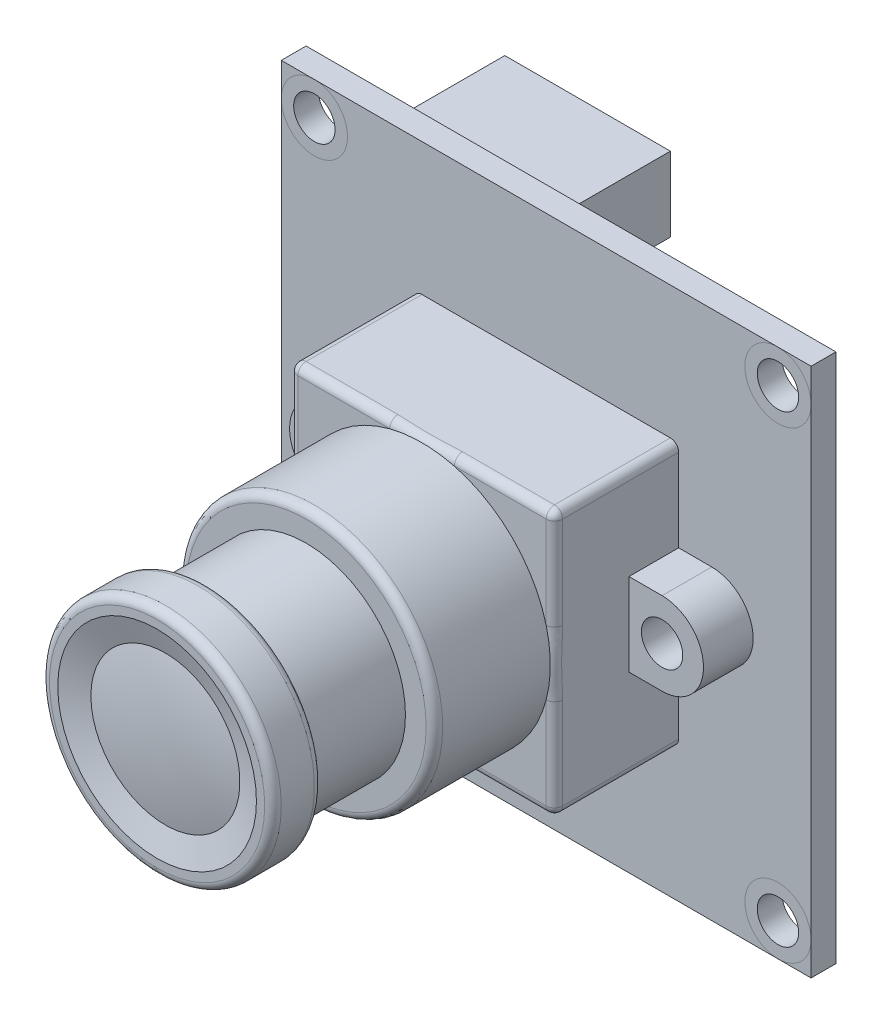
SolidWorks part; units mm, degrees
ref_plane "Front" through (0, 0, 0) normal (0, 0, 1) x (1, 0, 0)
ref_plane "Top" through (0, 0, 0) normal (0, 1, 0) x (1, 0, 0)
ref_plane "Right" through (0, 0, 0) normal (1, 0, 0) x (0, 0, -1)
sketch "Sketch1" plane through (0, 0, 0) normal (0, 0, 1) x (1, 0, 0)
  line L1 (-16, -16) -> (16, -16)
  line L2 (-16, -16) -> (-16, 16)
  line L3 (-16, 16) -> (16, 16)
  line L4 (16, -16) -> (16, 16)
  line L5 (-16, -16) -> (16, 16) construction
  line L6 (-16, 16) -> (16, -16) construction
  point P0 (0, 0)
  dimension "D1" = 32
extrude "Boss-Extrude1" add sketch "Sketch1" along normal blind 1.5
sketch "Sketch2" plane through (0, 0, 1.5) normal (0, 0, 1) x (1, 0, 0)
  line L0 (0, 16) -> (0, -16) construction
  line L1 (16, 16) -> (-16, 16) construction
  line L2 (-16, -16) -> (16, -16) construction
  line L3 (16, 0) -> (-16, 0) construction
  line L4 (16, -16) -> (16, 16) construction
  line L5 (-16, 16) -> (-16, -16) construction
  line L6 (-14, 14) -> (-14, 16) construction
  line L7 (-14, 14) -> (-16, 14) construction
  circle A0 centre (-14, 14) radius 1.25
  circle A1 centre (14, 14) radius 1.25
  circle A2 centre (14, -14) radius 1.25
  circle A3 centre (-14, -14) radius 1.25
  point P26 (0, 0)
  dimension "D1" = 2.5
  dimension "D2" = 28
  dimension "D3" = 4
extrude "Cut-Extrude1" cut sketch "Sketch2" against normal through all
sketch "Sketch3" plane through (0, 0, 1.5) normal (0, 0, 1) x (1, 0, 0)
  line L1 (8, -8) -> (-8, -8)
  line L2 (8, -8) -> (8, 8)
  line L3 (8, 8) -> (-8, 8)
  line L4 (-8, -8) -> (-8, 8)
  line L5 (8, -8) -> (-8, 8) construction
  line L6 (8, 8) -> (-8, -8) construction
  point P0 (0, 0)
  dimension "D1" = 16
extrude "Boss-Extrude2" add sketch "Sketch3" along normal blind 7.5
sketch "Sketch4" plane through (0, 0, 1.5) normal (0, 0, 1) x (1, 0, 0)
  line L0 (0, 0) -> (-10, 0) construction
  line L1 (-10, 2.5) -> (-8, 2.5)
  line L2 (-8, 8) -> (-8, -8) construction
  line L3 (-10, -2.5) -> (-8, -2.5)
  line L4 (-8, 2.5) -> (-8, -2.5)
  line L5 (0, 0) -> (0, 8) construction
  line L6 (8, 8) -> (-8, 8) construction
  line L7 (10, -2.5) -> (8, -2.5)
  line L8 (8, 2.5) -> (8, -2.5)
  line L9 (10, 2.5) -> (8, 2.5)
  circle A0 centre (-10, 0) radius 1.25
  circle A1 centre (-10, 0) radius 2.5 construction
  arc A2 (-10, 2.5) -> (-10, -2.5) centre (-10, 0) ccw
  circle A3 centre (10, 0) radius 1.25
  arc A4 (10, 2.5) -> (10, -2.5) centre (10, 0) cw
  point P5 (-9, 2.5)
  dimension "D2" = 2.5
  dimension "D3" = 5
  dimension "D1" = 10
extrude "Boss-Extrude3" add sketch "Sketch4" along normal blind 3
sketch "Sketch5" plane through (0, 0, 9) normal (0, 0, 1) x (1, 0, 0)
  circle A0 centre (0, 0) radius 7.75
  dimension "D1" = 15.5
extrude "Boss-Extrude4" add sketch "Sketch5" along normal blind 7
sketch "Sketch6" plane through (0, 0, 16) normal (0, 0, 1) x (1, 0, 0)
  circle A0 centre (0, 0) radius 6
  dimension "D1" = 12
extrude "Boss-Extrude5" add sketch "Sketch6" along normal blind 6
sketch "Sketch8" plane through (0, 0, 0) normal (0, 1, 0) x (1, 0, 0)
  line L0 (0, -22) -> (-7, -22)
  line L1 (-6, -22) -> (6, -22) construction
  line L2 (-7, -22) -> (-7, -25)
  line L3 (-7, -25) -> (-6, -25)
  line L4 (-6, -25) -> (-4.5, -24.5)
  line L5 (-4.5, -24.5) -> (0, -24.5) construction
  line L6 (0, -24.5) -> (0, -22) construction
  line L7 (-6, -25) -> (0, -25) construction
  line L8 (0, -25) -> (0, -24.5) construction
  line L9 (0, -22) -> (0, -25)
  circle A0 centre (0, -4.5) radius 20.5 construction
  arc A1 (0, -25) -> (-4.5, -24.5) centre (0, -4.5) cw
  dimension "D1" = 14
  dimension "D2" = 3
  dimension "D3" = 0.5
  dimension "D4" = 1.5
  dimension "D5" = 1
revolve "Revolve1" add sketch "Sketch8" angle 360 about L9
sketch "Sketch9" plane through (0, 0, 0) normal (0, 0, -1) x (-1, 0, 0)
  line L0 (16, 16) -> (16, -16) construction
  line L1 (10, 11) -> (0, 11)
  line L2 (10, 11) -> (10, 15.5)
  line L3 (10, 15.5) -> (0, 15.5)
  line L4 (0, 11) -> (0, 15.5)
  line L5 (10, 11) -> (0, 15.5) construction
  line L6 (10, 15.5) -> (0, 11) construction
  line L7 (-16, 16) -> (16, 16) construction
  point P0 (5, 13.25)
  dimension "D1" = 10
  dimension "D2" = 4.5
  dimension "D3" = 6
  dimension "D4" = 0.5
extrude "Boss-Extrude6" add sketch "Sketch9" along normal blind 6
fillet "Fillet1" radius 0.5 4 edges at (-8, -8, 5.25) (-8, 8, 5.25) (8, -8, 5.25) (8, 8, 5.25)
fillet "Fillet2" radius 0.5 11 edges at (7.8536, 7.8536, 9) (8, 0, 9) (7.8536, -7.8536, 9) (0, -8, 9) (-7.8536, -7.8536, 9) (-8, 0, 9) (-7.8536, 7.8536, 9) (0, 8, 9) (-7, 0, 22) (-7, 0, 25) (7.75, 0, 16)
sketch "Sketch10" plane through (0, 0, 1.5) normal (0, 0, 1) x (1, 0, 0)
  circle A0 centre (-14, 14) radius 2
  circle A1 centre (14, 14) radius 2
  circle A2 centre (14, -14) radius 2
  circle A3 centre (-14, -14) radius 2
split line "Split Line1"
